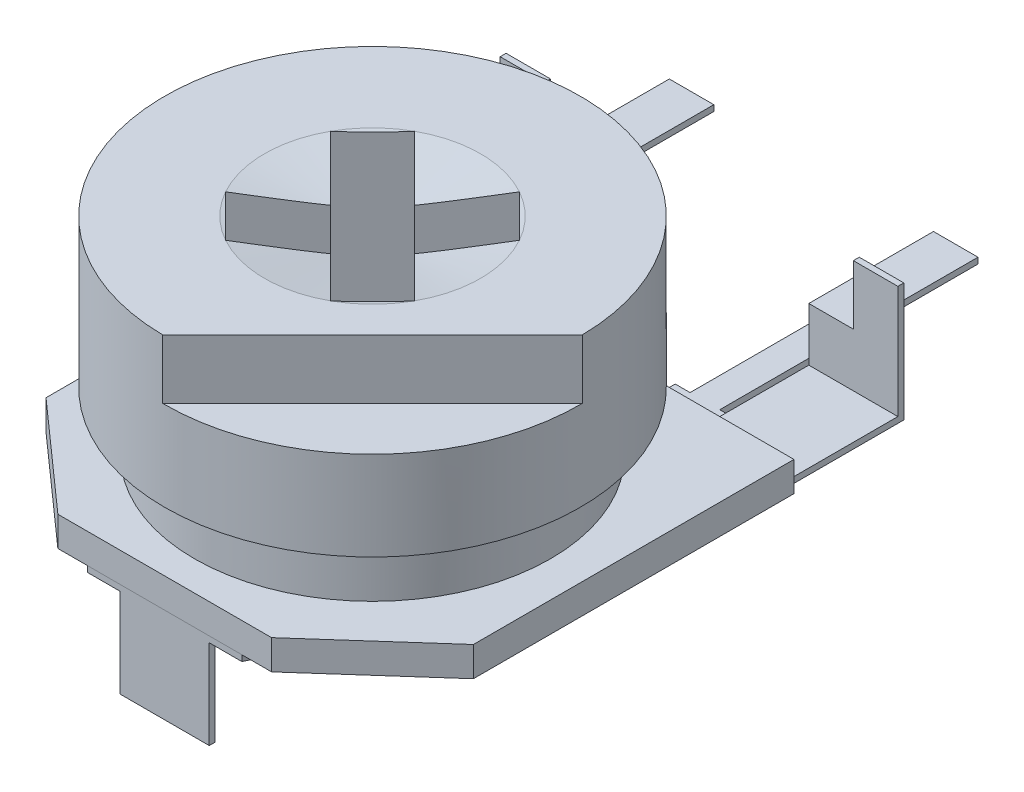
SolidWorks part; units mm, degrees
ref_plane "Front Plane" through (0, 0, 0) normal (0, 0, 1) x (1, 0, 0)
ref_plane "Top Plane" through (0, 0, 0) normal (0, 1, 0) x (1, 0, 0)
ref_plane "Right Plane" through (0, 0, 0) normal (1, 0, 0) x (0, 0, -1)
sketch "Sketch1" plane through (0, 0, 0) normal (0, 1, 0) x (1, 0, 0)
  line L0 (0.8839, 1.591) -> (0, 0.7071)
  line L1 (0.8839, 1.591) -> (1.591, 0.8839)
  line L2 (-1.591, -0.8839) -> (-0.8839, -1.591)
  line L3 (1.591, 0.8839) -> (0.7071, 0)
  line L4 (0.8839, 1.591) -> (-0.8839, -1.591) construction
  line L5 (-1.591, -0.8839) -> (1.591, 0.8839) construction
  line L6 (-0.8839, 1.591) -> (0, 0.7071)
  line L7 (-0.8839, 1.591) -> (-1.591, 0.8839)
  line L8 (1.591, -0.8839) -> (0.8839, -1.591)
  line L9 (-1.591, 0.8839) -> (-0.7071, 0)
  line L10 (-0.8839, 1.591) -> (0.8839, -1.591) construction
  line L11 (1.591, -0.8839) -> (-1.591, 0.8839) construction
  line L12 (0.7071, 0) -> (1.591, -0.8839)
  line L13 (0, -0.7071) -> (-0.8839, -1.591)
  line L14 (0, -0.7071) -> (0.8839, -1.591)
  line L15 (-0.7071, 0) -> (-1.591, -0.8839)
  line L16 (3.4998, 0.0357) -> (-0.0357, -3.4998) construction
  circle A0 centre (0, 0) radius 3.5
  point P3 (1.4719, 0.9898)
  point P16 (0, 0)
  dimension "D3" = 7
  dimension "D1" = 3.5
  dimension "D2" = 1
  dimension "D4" = 5
extrude "Boss-Extrude1" add sketch "Sketch1" against normal blind 2.5
sketch "Sketch2" plane through (0, 0, 0) normal (0, 1, 0) x (1, 0, 0)
  line L0 (3.4998, 0.0357) -> (-0.0357, -3.4998)
  arc A0 (-0.0357, -3.4998) -> (3.4998, 0.0357) centre (0, 0) ccw
  circle M13 centre (0, 0) radius 3.5
extrude "Cut-Extrude1" cut sketch "Sketch2" against normal blind 1 contours L0 M13
sketch "Sketch3" plane through (0, 0, 0) normal (0, 1, 0) x (1, 0, 0)
  circle A0 centre (0, 0) radius 1.82
extrude "Cut-Extrude2" cut sketch "Sketch3" against normal blind 1 draft 80
sketch "Sketch4" plane through (0, -2.5, 0) normal (0, -1, 0) x (1, 0, 0)
  circle A0 centre (0, 0) radius 3
  circle A1 centre (0, 0) radius 3.5 construction
  dimension "D1" = 0.5
extrude "Boss-Extrude2" add sketch "Sketch4" along normal blind 1
fillet "Fillet1" radius 0.25 1 edges at (0, -2.5, -3)
sketch "Sketch5" plane through (0, -3.5, 0) normal (0, -1, 0) x (1, 0, 0)
  line L0 (1.8, 3.5) -> (3.6, 1.9)
  line L1 (-3.6, -3.5) -> (3.6, -3.5)
  line L2 (-3.6, -3.5) -> (-3.6, 1.9)
  line L3 (-1.8, 3.5) -> (1.8, 3.5)
  line L4 (3.6, -3.5) -> (3.6, 1.9)
  line L5 (-3.6, 1.9) -> (-1.8, 3.5)
  arc A0 (-0.0357, 3.4998) -> (3.4998, -0.0357) centre (0, 0) ccw construction
  circle A1 centre (0, 0) radius 1
  point P7 (0, -3.5)
  dimension "D1" = 3.6
  dimension "D4" = 2
  dimension "D2" = 3.6
  dimension "D3" = 5.4
extrude "Boss-Extrude3" add sketch "Sketch5" along normal blind 0.5 separate body
sketch "Sketch6" plane through (0, -4, 0) normal (0, -1, 0) x (1, 0, 0)
  line L0 (-1.3, 3.5) -> (-2, 2)
  line L1 (-3.35, -2) -> (-1.85, -2)
  line L2 (-3.35, -2) -> (-3.35, -5.5)
  line L3 (-3.35, -5.5) -> (-1.85, -5.5)
  line L4 (-1.85, -2) -> (-1.85, -5.5)
  line L5 (1.8, 3.5) -> (-1.8, 3.5) construction
  line L6 (-2, 2) -> (-2, -0.5)
  line L7 (-2, -0.5) -> (-1, -1.618)
  line L8 (-1, -1.618) -> (-1, -3.5)
  line L9 (-1, -3.5) -> (1, -3.5)
  line L10 (-1.3, 3.5) -> (1.3, 3.5)
  line L11 (0, 3.5) -> (0, -3.5) construction
  line L12 (-3.6, -3.5) -> (3.6, -3.5) construction
  line L13 (-3.6, 1.9) -> (-3.6, -3.5) construction
  line L14 (1, -1.618) -> (1, -3.5)
  line L15 (2, -0.5) -> (1, -1.618)
  line L16 (2, 2) -> (2, -0.5)
  line L17 (1.85, -2) -> (1.85, -5.5)
  line L18 (3.35, -5.5) -> (1.85, -5.5)
  line L19 (3.35, -2) -> (3.35, -5.5)
  line L20 (3.35, -2) -> (1.85, -2)
  line L21 (1.3, 3.5) -> (2, 2)
  circle A0 centre (0, 0) radius 1
  circle A1 centre (0, 0) radius 1 construction
  point P22 (0, -3.5)
  dimension "D1" = 0.5
  dimension "D2" = 1.5
  dimension "D3" = 0.25
  dimension "D4" = 1.5
  dimension "D5" = 3.5
  dimension "D6" = 2.5
  dimension "D7" = 2
  dimension "D8" = 1.5
  dimension "D9" = 1.5
  dimension "D10" = 1
extrude "Boss-Extrude4" add sketch "Sketch6" along normal blind 0.1 separate body
sketch "Sketch7" plane through (0, -4.1, 0) normal (0, -1, 0) x (1, 0, 0)
  line L0 (1.3, 3.5) -> (-1.3, 3.5) construction
  line L1 (-0.75, 3.5) -> (0.75, 3.5)
  line L2 (-0.75, 3.5) -> (-0.75, 3.4)
  line L3 (-0.75, 3.4) -> (0.75, 3.4)
  line L4 (0.75, 3.5) -> (0.75, 3.4)
  line L5 (1.8, 3.5) -> (-1.8, 3.5) construction
  line L6 (-3.6, -3.5) -> (3.6, -3.5) construction
  line L7 (-1, -2.5) -> (1, -2.5)
  line L8 (-1, -2.5) -> (-1, -3.5)
  line L9 (-1, -3.5) -> (1, -3.5)
  line L10 (1, -2.5) -> (1, -3.5)
  line L11 (1, -3.5) -> (1, -1.618) construction
  line L12 (-1, -1.618) -> (-1, -3.5) construction
  point P8 (0, 3.5)
  point P9 (0, 3.5)
  point P15 (0, 0)
  point P16 (0, 0)
  dimension "D1" = 1.5
  dimension "D2" = 0.1
  dimension "D3" = 1
extrude "Boss-Extrude5" add sketch "Sketch7" along normal blind 1.5
sketch "Sketch8" plane through (0, 0, -5.5) normal (0, 0, -1) x (-1, 0, 0)
  line L0 (-1.85, -4.1) -> (-1.85, -4) construction
  line L1 (-3.35, -4.1) -> (-1.85, -4.1)
  line L2 (-3.35, -4.1) -> (-3.35, -2.1)
  line L3 (-2.6, -3.1) -> (-1.85, -3.1)
  line L4 (-1.85, -4.1) -> (-1.85, -3.1)
  line L6 (-2.6, -3.1) -> (-2.6, -2.1)
  line L7 (-2.6, -2.1) -> (-3.35, -2.1)
  line L9 (0, 0) -> (0, -5.1481) construction
  line L10 (3.35, -4.1) -> (1.85, -4.1)
  line L11 (1.85, -4.1) -> (1.85, -3.1)
  line L12 (2.6, -3.1) -> (1.85, -3.1)
  line L13 (2.6, -3.1) -> (2.6, -2.1)
  line L14 (2.6, -2.1) -> (3.35, -2.1)
  line L15 (3.35, -4.1) -> (3.35, -2.1)
  point P11 (-3.35, -3.1)
  point P13 (-2.6, -4.1)
  dimension "D1" = 2
extrude "Boss-Extrude6" add sketch "Sketch8" along normal blind 0.1
sketch "Sketch9" plane through (0, 0, -5.6) normal (0, 0, -1) x (-1, 0, 0)
  line L0 (-1.85, -4.1) -> (-1.85, -3.1) construction
  line L1 (-2.6, -3.1) -> (-1.85, -3.1)
  line L2 (-2.6, -3.1) -> (-2.6, -3.2)
  line L3 (-2.6, -3.2) -> (-1.85, -3.2)
  line L4 (-1.85, -3.1) -> (-1.85, -3.2)
  line L5 (1.85, -3.1) -> (1.85, -4.1) construction
  line L6 (2.6, -3.1) -> (1.85, -3.1)
  line L7 (2.6, -3.1) -> (2.6, -3.2)
  line L8 (2.6, -3.2) -> (1.85, -3.2)
  line L9 (1.85, -3.1) -> (1.85, -3.2)
  dimension "D1" = 0.1
extrude "Boss-Extrude7" add sketch "Sketch9" along normal blind 2
sketch "Sketch11" plane through (0, 0, -3.5) normal (0, 0, -1) x (-1, 0, 0)
  line L0 (1, -5.6) -> (-1, -5.6) construction
  line L1 (0.5, -5.6) -> (-0.5, -5.6)
  line L2 (0.5, -5.6) -> (0.5, -5.5)
  line L3 (0.5, -5.5) -> (-0.5, -5.5)
  line L4 (-0.5, -5.6) -> (-0.5, -5.5)
  point P6 (0, -5.5)
  dimension "D1" = 1
  dimension "D2" = 0.1
extrude "Boss-Extrude8" add sketch "Sketch11" along normal up to surface (2.1 mm away) up to face at (-2.6, -3.1286, -5.6)
sketch "Sketch12" plane through (0, 0, -5.6) normal (0, 0, -1) x (-1, 0, 0)
  line L0 (0.5, -5.6) -> (-0.5, -5.6) construction
  line L1 (0.25, -5.6) -> (-0.25, -5.6)
  line L2 (0.25, -5.6) -> (0.25, -5.5)
  line L3 (0.25, -5.5) -> (-0.25, -5.5)
  line L4 (-0.25, -5.6) -> (-0.25, -5.5)
  line L5 (-0.5, -5.5) -> (0.5, -5.5) construction
  line L6 (-1, -5.6) -> (1, -5.6) construction
  point P8 (0, -5.6)
  point P11 (0, -5.6)
  dimension "D1" = 0.5
extrude "Boss-Extrude9" add sketch "Sketch12" along normal up to surface (2 mm away) up to face at (-2.225, -3.15, -7.6)
sketch "Sketch13" plane through (0, -3.5, 0) normal (0, -1, 0) x (1, 0, 0)
  line L0 (-0.5079, -0.8614) -> (0.8614, 0.5079)
  line L1 (-0.8614, -0.5079) -> (0.5079, 0.8614)
  line L2 (-1.591, -0.8839) -> (-0.7071, 0) construction
  arc A0 (-0.5079, -0.8614) -> (0.8614, 0.5079) centre (0, 0) ccw
  circle A1 centre (0, 0) radius 1 construction
  arc A2 (0.5079, 0.8614) -> (-0.8614, -0.5079) centre (0, 0) ccw
  dimension "D1" = 0.5
extrude "Boss-Extrude10" add sketch "Sketch13" along normal blind 0.8 separate body
